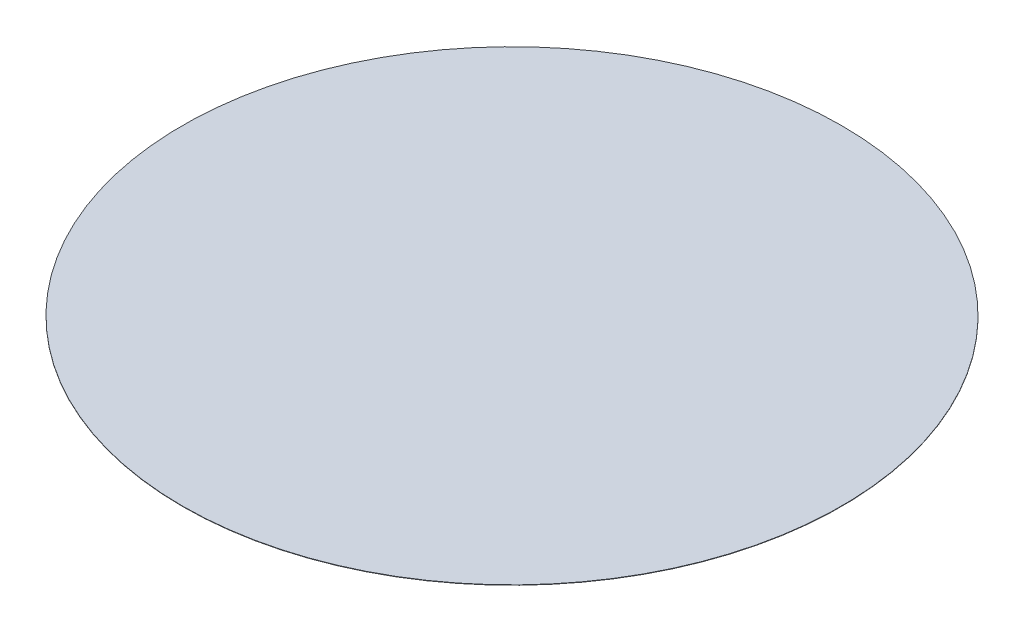
SolidWorks part; units mm, degrees
material "201 Annealed Stainless Steel (SS)"
ref_plane "Front Plane" through (0, 0, 0) normal (0, 0, 1) x (1, 0, 0)
ref_plane "Top Plane" through (0, 0, 0) normal (0, 1, 0) x (1, 0, 0)
ref_plane "Right Plane" through (0, 0, 0) normal (1, 0, 0) x (0, 0, -1)
sketch "Sketch1" plane through (0, 0, 0) normal (0, 1, 0) x (1, 0, 0)
  circle A0 centre (0, 0) radius 22.5
  dimension "D1" = 45
extrude "Boss-Extrude1" add sketch "Sketch1" along normal blind 0.0254
